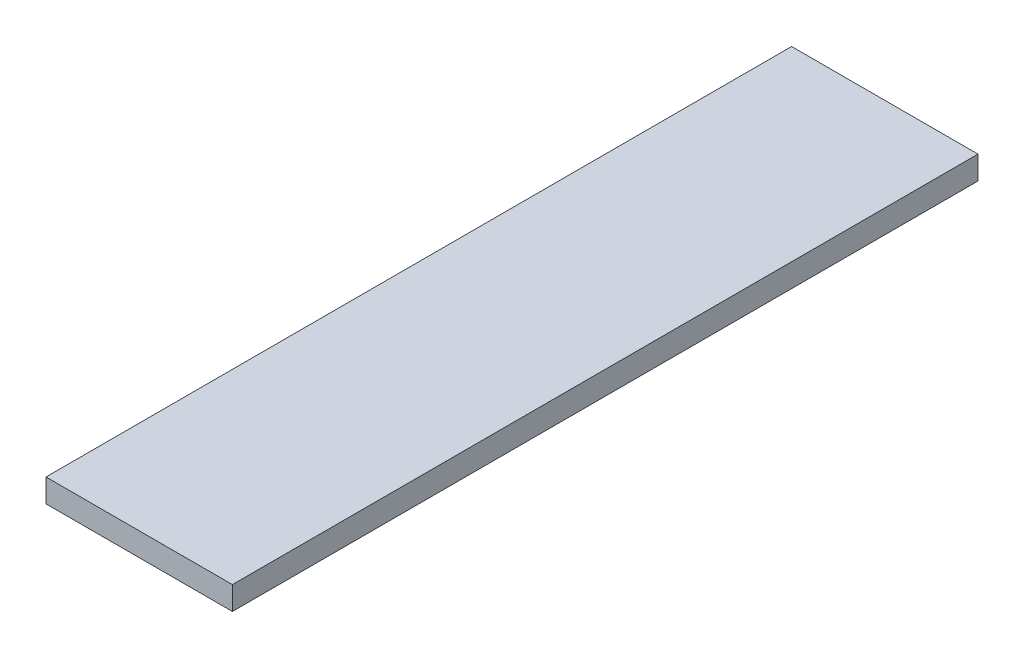
SolidWorks part; units mm, degrees
ref_plane "Front Plane" through (0, 0, 0) normal (0, 0, 1) x (1, 0, 0)
ref_plane "Top Plane" through (0, 0, 0) normal (0, 1, 0) x (1, 0, 0)
ref_plane "Right Plane" through (0, 0, 0) normal (1, 0, 0) x (0, 0, -1)
sketch "Sketch1" plane through (0, 0, 0) normal (0, 1, 0) x (1, 0, 0)
  line L1 (0, 0) -> (25.4, 0)
  line L2 (0, 0) -> (0, 101.6)
  line L3 (0, 101.6) -> (25.4, 101.6)
  line L4 (25.4, 0) -> (25.4, 101.6)
  dimension "D1" = 101.6
  dimension "D2" = 25.4
extrude "Boss-Extrude1" add sketch "Sketch1" along normal blind 3.175
